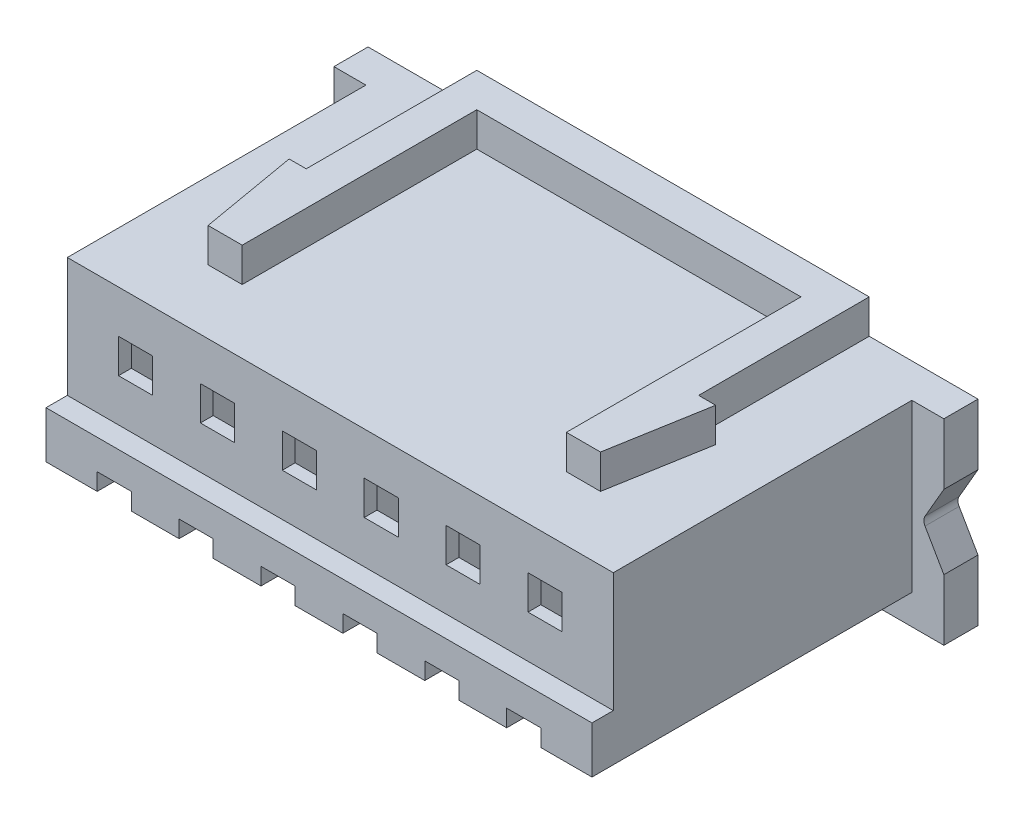
SolidWorks part; units mm, degrees
ref_plane "Front Plane" through (0, 0, 0) normal (0, 0, 1) x (1, 0, 0)
ref_plane "Top Plane" through (0, 0, 0) normal (0, 1, 0) x (1, 0, 0)
ref_plane "Right Plane" through (0, 0, 0) normal (1, 0, 0) x (0, 0, -1)
sketch "Sketch1" plane through (0, 0, 0) normal (0, 0, 1) x (1, 0, 0)
  line L1 (-6.4, -2.15) -> (6.4, -2.15)
  line L2 (-6.4, -2.15) -> (-6.4, 2.15)
  line L3 (-6.4, 2.15) -> (6.4, 2.15)
  line L4 (6.4, -2.15) -> (6.4, 2.15)
  line L5 (-6.4, -2.15) -> (6.4, 2.15) construction
  line L6 (-6.4, 2.15) -> (6.4, -2.15) construction
  point P0 (0, 0)
  dimension "D1" = 4.3
  dimension "D2" = 12.8
extrude "Boss-Extrude1" add sketch "Sketch1" along normal blind 7
sketch "Sketch2" plane through (0, 0, 0) normal (0, 0, -1) x (-1, 0, 0)
  line L0 (0, 0) -> (0, 2.15) construction
  line L1 (-7.15, 2.15) -> (7.15, 2.15)
  line L2 (-7.15, 2.15) -> (-7.15, -2.45)
  line L3 (-7.15, -2.45) -> (7.15, -2.45)
  line L4 (7.15, 2.15) -> (7.15, -2.45)
  dimension "D1" = 14.3
  dimension "D2" = 4.6
extrude "Boss-Extrude2" add sketch "Sketch2" along normal blind 0.8
sketch "Sketch3" plane through (0, 0, 0) normal (0, 0, 1) x (1, 0, 0)
  line L1 (7.15, 2.15) -> (7.15, -2.45) construction
  line L2 (6.65, -0.15) -> (7.15, -1.016)
  line L3 (6.65, -0.15) -> (7.15, 0.716)
  line L4 (7.15, -0.15) -> (6.65, -0.15) construction
  line L5 (7.15, 0.716) -> (7.15, -1.016)
  dimension "D1" = 60
  dimension "D2" = 0.5
  dimension "D3" = 60
extrude "Cut-Extrude1" cut sketch "Sketch3" against normal blind 1
fillet "Fillet1" radius 0.2 1 edges at (6.65, -0.15, -0.4)
sketch "Sketch4" plane through (0, 0, 7) normal (0, 0, 1) x (1, 0, 0)
  line L0 (-6.4, 2.15) -> (-6.4, -2.15) construction
  line L1 (-6.4, -0.65) -> (6.4, -0.65)
  line L2 (-6.4, -0.65) -> (-6.4, -2.15)
  line L3 (-6.4, -2.15) -> (6.4, -2.15)
  line L4 (6.4, -0.65) -> (6.4, -2.15)
  dimension "D1" = 1.5
extrude "Boss-Extrude3" add sketch "Sketch4" along normal blind 0.5
sketch "Sketch5" plane through (0, 0, 7.5) normal (0, 0, 1) x (1, 0, 0)
  line L1 (3.28, -1.35) -> (3.28, -2.15)
  line L2 (2.48, -1.35) -> (3.28, -1.35)
  line L3 (2.48, -1.35) -> (2.48, -2.15)
  line L4 (2.48, -2.15) -> (3.28, -2.15)
  line L6 (1.36, -1.35) -> (1.36, -2.15)
  line L7 (0.56, -1.35) -> (1.36, -1.35)
  line L8 (0.56, -1.35) -> (0.56, -2.15)
  line L9 (0.56, -2.15) -> (1.36, -2.15)
  line L10 (-0.56, -1.35) -> (-0.56, -2.15)
  line L11 (-1.36, -1.35) -> (-0.56, -1.35)
  line L12 (-1.36, -1.35) -> (-1.36, -2.15)
  line L13 (-1.36, -2.15) -> (-0.56, -2.15)
  line L14 (4.4, -1.35) -> (5.2, -1.35)
  line L15 (5.2, -1.35) -> (5.2, -2.15)
  line L16 (4.4, -1.35) -> (4.4, -2.15)
  line L17 (4.4, -2.15) -> (5.2, -2.15)
  line L18 (6.4, -2.15) -> (6.4, -0.65) construction
  line L20 (-2.48, -1.35) -> (-2.48, -2.15)
  line L21 (-3.28, -1.35) -> (-2.48, -1.35)
  line L22 (-3.28, -1.35) -> (-3.28, -2.15)
  line L23 (-3.28, -2.15) -> (-2.48, -2.15)
  line L24 (-4.4, -1.35) -> (-4.4, -2.15)
  line L25 (-5.2, -1.35) -> (-4.4, -1.35)
  line L26 (-5.2, -1.35) -> (-5.2, -2.15)
  line L27 (-5.2, -2.15) -> (-4.4, -2.15)
  line L29 (-6.4, 2.15) -> (-6.4, -2.15) construction
  dimension "D1" = 0.8
  dimension "D2" = 0.8
  dimension "D3" = 6
  dimension "D5" = 1.2
  dimension "D4" = 1.2
extrude "Cut-Extrude2" cut sketch "Sketch5" against normal blind 3.2
sketch "Sketch6" plane through (0, 0, 7) normal (0, 0, 1) x (1, 0, 0)
  line L0 (-6.4, 2.15) -> (-6.4, -0.65) construction
  line L1 (-5.2, 1.15) -> (-4.4, 1.15)
  line L2 (-5.2, 1.15) -> (-5.2, 0.35)
  line L3 (-5.2, 0.35) -> (-4.4, 0.35)
  line L4 (-4.4, 1.15) -> (-4.4, 0.35)
  line L5 (-3.28, 0.35) -> (-2.48, 0.35)
  line L6 (-2.48, 1.15) -> (-2.48, 0.35)
  line L7 (-3.28, 1.15) -> (-2.48, 1.15)
  line L8 (-3.28, 1.15) -> (-3.28, 0.35)
  line L9 (-1.36, 0.35) -> (-0.56, 0.35)
  line L10 (-0.56, 1.15) -> (-0.56, 0.35)
  line L11 (-1.36, 1.15) -> (-0.56, 1.15)
  line L12 (-1.36, 1.15) -> (-1.36, 0.35)
  line L13 (0.56, 0.35) -> (1.36, 0.35)
  line L14 (1.36, 1.15) -> (1.36, 0.35)
  line L15 (0.56, 1.15) -> (1.36, 1.15)
  line L16 (0.56, 1.15) -> (0.56, 0.35)
  line L18 (6.4, 2.15) -> (-6.4, 2.15) construction
  line L19 (2.48, 0.35) -> (3.28, 0.35)
  line L20 (3.28, 1.15) -> (3.28, 0.35)
  line L21 (2.48, 1.15) -> (3.28, 1.15)
  line L22 (2.48, 1.15) -> (2.48, 0.35)
  line L23 (4.4, 0.35) -> (5.2, 0.35)
  line L24 (5.2, 1.15) -> (5.2, 0.35)
  line L25 (4.4, 1.15) -> (5.2, 1.15)
  line L26 (4.4, 1.15) -> (4.4, 0.35)
  line L27 (6.4, -0.65) -> (6.4, 2.15) construction
  dimension "D1" = 0.8
  dimension "D2" = 0.8
  dimension "D3" = 1.2
  dimension "D5" = 1.2
  dimension "D6" = 1
  dimension "D4" = 6
extrude "Cut-Extrude3" cut sketch "Sketch6" against normal blind 10
sketch "Sketch7" plane through (0, 2.15, 0) normal (0, 1, 0) x (1, 0, 0)
  line L0 (-4.6, -5.5) -> (-5, -3.2)
  line L1 (-5, -3.2) -> (-4.6, -3.2)
  line L2 (-4.6, -3.2) -> (-4.6, 0.8)
  line L3 (-7.15, 0.8) -> (7.15, 0.8) construction
  line L4 (-4.6, 0.8) -> (4.6, 0.8)
  line L5 (4.6, 0.8) -> (4.6, -3.2)
  line L6 (4.6, -3.2) -> (5, -3.2)
  line L7 (5, -3.2) -> (4.6, -5.5)
  line L8 (4.6, -5.5) -> (3.8, -5.5)
  line L9 (3.8, -5.5) -> (3.8, 0)
  line L10 (3.8, 0) -> (-3.8, 0)
  line L11 (-3.8, 0) -> (-3.8, -5.5)
  line L12 (-3.8, -5.5) -> (-4.6, -5.5)
  line L13 (0, 0) -> (0, 0.8) construction
  dimension "D1" = 0.8
  dimension "D2" = 0.8
  dimension "D3" = 0.8
  dimension "D4" = 0.8
  dimension "D5" = 1.2
  dimension "D6" = 4
  dimension "D7" = 2.3
  dimension "D8" = 4
  dimension "D9" = 1.2
  dimension "D10" = 0.8
  dimension "D11" = 9.2
extrude "Boss-Extrude4" add sketch "Sketch7" along normal blind 0.8
sketch "Sketch8" plane through (0, 0, -0.8) normal (0, 0, -1) x (-1, 0, 0)
  line L1 (5.8, 1.85) -> (3.88, 1.85)
  line L2 (5.8, 1.85) -> (5.8, -0.95)
  line L3 (5.2, -0.95) -> (5.2, -1.35)
  line L4 (3.8, 1.85) -> (3.8, -0.95)
  line L5 (5.8, -0.95) -> (5.2, -0.95)
  line L6 (5.2, -1.35) -> (4.4, -1.35)
  line L7 (4.4, -1.35) -> (4.4, -0.95)
  line L8 (4.4, -0.95) -> (3.88, -0.95)
  line L10 (3.28, -0.95) -> (3.28, -1.35)
  line L11 (3.8, -0.95) -> (3.28, -0.95)
  line L12 (3.88, 1.85) -> (3.88, -0.95)
  line L13 (3.8, 1.85) -> (1.96, 1.85)
  line L14 (1.88, 1.85) -> (1.88, -0.95)
  line L15 (2.48, -0.95) -> (1.96, -0.95)
  line L16 (2.48, -1.35) -> (2.48, -0.95)
  line L17 (3.28, -1.35) -> (2.48, -1.35)
  line L18 (1.36, -0.95) -> (1.36, -1.35)
  line L19 (1.88, -0.95) -> (1.36, -0.95)
  line L20 (1.96, 1.85) -> (1.96, -0.95)
  line L21 (1.88, 1.85) -> (0.04, 1.85)
  line L22 (-0.04, 1.85) -> (-0.04, -0.95)
  line L23 (0.56, -0.95) -> (0.04, -0.95)
  line L24 (0.56, -1.35) -> (0.56, -0.95)
  line L25 (1.36, -1.35) -> (0.56, -1.35)
  line L26 (-0.56, -0.95) -> (-0.56, -1.35)
  line L27 (-0.04, -0.95) -> (-0.56, -0.95)
  line L28 (0.04, 1.85) -> (0.04, -0.95)
  line L29 (-0.04, 1.85) -> (-1.88, 1.85)
  line L30 (-1.96, 1.85) -> (-1.96, -0.95)
  line L31 (-1.36, -0.95) -> (-1.88, -0.95)
  line L32 (-1.36, -1.35) -> (-1.36, -0.95)
  line L33 (-0.56, -1.35) -> (-1.36, -1.35)
  line L34 (-2.48, -0.95) -> (-2.48, -1.35)
  line L35 (-1.96, -0.95) -> (-2.48, -0.95)
  line L37 (-1.88, 1.85) -> (-1.88, -0.95)
  line L38 (-1.96, 1.85) -> (-3.8, 1.85)
  line L39 (-3.88, 1.85) -> (-3.88, -0.95)
  line L40 (-3.28, -0.95) -> (-3.8, -0.95)
  line L41 (-3.28, -1.35) -> (-3.28, -0.95)
  line L42 (-2.48, -1.35) -> (-3.28, -1.35)
  line L43 (-4.4, -0.95) -> (-4.4, -1.35)
  line L44 (-3.88, -0.95) -> (-4.4, -0.95)
  line L45 (-3.8, 1.85) -> (-3.8, -0.95)
  line L46 (-3.88, 1.85) -> (-5.8, 1.85)
  line L47 (-5.8, 1.85) -> (-5.8, -0.95)
  line L48 (-5.2, -0.95) -> (-5.8, -0.95)
  line L49 (-5.2, -1.35) -> (-5.2, -0.95)
  line L50 (-4.4, -1.35) -> (-5.2, -1.35)
  line L52 (-6.4, -2.15) -> (-6.4, 2.15) construction
  dimension "D1" = 2.8
  dimension "D2" = 2
  dimension "D3" = 0.4
  dimension "D4" = 6
  dimension "D5" = 0.6
  dimension "D6" = 0.6
  dimension "D7" = 0.6
extrude "Cut-Extrude4" cut sketch "Sketch8" against normal blind 7.5
sketch "Sketch9" plane through (0, -2.15, 0) normal (0, -1, 0) x (1, 0, 0)
  line L20 (5.2, 4.3) -> (4.4, 4.3)
  line L21 (4.4, 4.3) -> (4.4, 7.5)
  line L22 (4.4, 7.5) -> (3.28, 7.5)
  line L31 (-5.2, 7.5) -> (-6.4, 7.5)
  line L32 (-5.2, 7.5) -> (-6.4, 7.5)
  line L33 (-4.4, 4.3) -> (-5.2, 4.3)
  line L34 (-4.4, 4.3) -> (-5.2, 4.3)
  line L35 (-6.4, 7.5) -> (-6.4, 0)
  line L36 (-6.4, 0) -> (6.4, 0)
  line L37 (6.4, 0) -> (6.4, 7.5)
  line L38 (6.4, 7.5) -> (5.2, 7.5)
  line L39 (5.2, 7.5) -> (5.2, 4.3)
  line L40 (5.2, 4.3) -> (4.4, 4.3)
  line L41 (4.4, 4.3) -> (4.4, 7.5)
  line L42 (4.4, 7.5) -> (3.28, 7.5)
  line L43 (-5.2, 4.3) -> (-5.2, 7.5)
  line L44 (-5.2, 4.3) -> (-5.2, 7.5)
  line L45 (3.28, 7.5) -> (3.28, 4.3)
  line L46 (3.28, 7.5) -> (3.28, 4.3)
  line L47 (3.28, 4.3) -> (2.48, 4.3)
  line L48 (3.28, 4.3) -> (2.48, 4.3)
  line L49 (2.48, 4.3) -> (2.48, 7.5)
  line L50 (2.48, 4.3) -> (2.48, 7.5)
  line L51 (2.48, 7.5) -> (1.36, 7.5)
  line L52 (2.48, 7.5) -> (1.36, 7.5)
  line L53 (1.36, 7.5) -> (1.36, 4.3)
  line L54 (1.36, 7.5) -> (1.36, 4.3)
  line L55 (-6.4, 7.5) -> (-6.4, 0)
  line L56 (-6.4, 0) -> (6.4, 0)
  line L57 (6.4, 0) -> (6.4, 7.5)
  line L58 (6.4, 7.5) -> (5.2, 7.5)
  line L59 (5.2, 7.5) -> (5.2, 4.3)
  line L60 (1.36, 4.3) -> (0.56, 4.3)
  line L61 (1.36, 4.3) -> (0.56, 4.3)
  line L62 (0.56, 4.3) -> (0.56, 7.5)
  line L63 (0.56, 4.3) -> (0.56, 7.5)
  line L64 (0.56, 7.5) -> (-0.56, 7.5)
  line L65 (0.56, 7.5) -> (-0.56, 7.5)
  line L66 (-0.56, 7.5) -> (-0.56, 4.3)
  line L67 (-0.56, 7.5) -> (-0.56, 4.3)
  line L68 (-0.56, 4.3) -> (-1.36, 4.3)
  line L69 (-0.56, 4.3) -> (-1.36, 4.3)
  line L70 (-1.36, 4.3) -> (-1.36, 7.5)
  line L71 (-1.36, 4.3) -> (-1.36, 7.5)
  line L72 (-1.36, 7.5) -> (-2.48, 7.5)
  line L73 (-1.36, 7.5) -> (-2.48, 7.5)
  line L74 (-2.48, 7.5) -> (-2.48, 4.3)
  line L75 (-2.48, 7.5) -> (-2.48, 4.3)
  line L76 (-2.48, 4.3) -> (-3.28, 4.3)
  line L77 (-2.48, 4.3) -> (-3.28, 4.3)
  line L78 (-3.28, 4.3) -> (-3.28, 7.5)
  line L79 (-3.28, 4.3) -> (-3.28, 7.5)
  line L80 (-3.28, 7.5) -> (-4.4, 7.5)
  line L81 (-3.28, 7.5) -> (-4.4, 7.5)
  line L82 (-4.4, 7.5) -> (-4.4, 4.3)
  line L83 (-4.4, 7.5) -> (-4.4, 4.3)
  dimension "D1" = 0
extrude "Cut-Extrude5" cut sketch "Sketch9" against normal blind 0.4
sketch "Sketch10" plane through (0, 0, -0.8) normal (0, 0, -1) x (-1, 0, 0)
  line L0 (-6.3469, -1.9657) -> (6.2527, -1.9657) construction
  text T0 "       1        2        3        4        5        6" font "Century Gothic" height 0.5
extrude "Boss-Extrude5" add sketch "Sketch10" along normal blind 0.1
